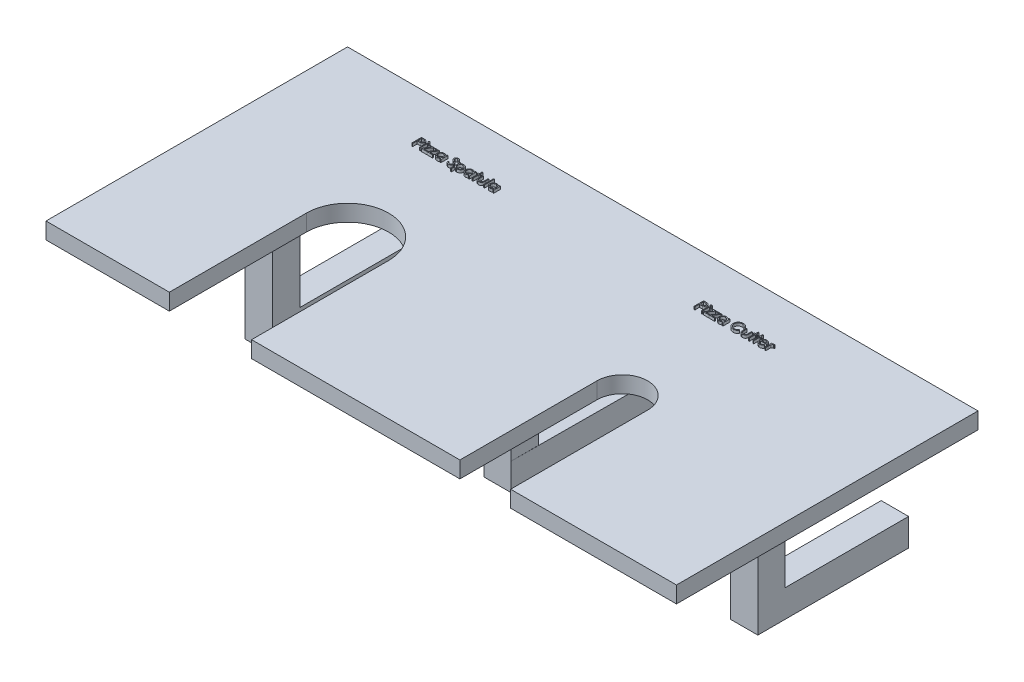
SolidWorks part; units mm, degrees
ref_plane "Front Plane" through (0, 0, 0) normal (0, 0, 1) x (1, 0, 0)
ref_plane "Top Plane" through (0, 0, 0) normal (0, 1, 0) x (1, 0, 0)
ref_plane "Right Plane" through (0, 0, 0) normal (1, 0, 0) x (0, 0, -1)
sketch "Sketch2" plane through (0, 0, 0) normal (0, 1, 0) x (1, 0, 0)
  line L0 (-88.9219, -70.4554) -> (-43.9219, -70.4554)
  line L1 (-88.9219, 39.5446) -> (141.0781, 39.5446)
  line L2 (-88.9219, 39.5446) -> (-88.9219, -70.4554)
  line L4 (141.0781, 39.5446) -> (141.0781, -70.4554)
  line L5 (-13.9219, -70.4554) -> (62.0781, -70.4554)
  line L6 (80.5781, -70.4554) -> (141.0781, -70.4554)
  line L8 (-43.9219, -70.4554) -> (-43.9219, -20.4554)
  line L9 (62.0781, -70.4554) -> (62.0781, -20.4554)
  line L12 (-13.9219, -20.4554) -> (-13.9219, -70.4554)
  line L13 (80.5781, -20.4554) -> (80.5781, -70.4554)
  arc A0 (-43.9219, -20.4554) -> (-13.9219, -20.4554) centre (-28.9219, -20.4554) cw
  arc A1 (62.0781, -20.4554) -> (80.5781, -20.4554) centre (71.3281, -20.4554) cw
  dimension "D1" = 230
  dimension "D2" = 110
extrude "Boss-Extrude2" add sketch "Sketch2" along normal blind 6
sketch3d "3DSketch1" plane through (0, 0, 0) normal (0, 0, 1) x (1, 0, 0)
sketch "Sketch6" plane through (0, 0, 15.4554) normal (0, 0, 1) x (1, 0, 0)
  line L5 (-71.2766, 0) -> (-61.2766, 0)
  line L6 (15.7975, 0) -> (25.7975, 0)
  line L7 (-88.9219, 0) -> (-43.9219, 0) construction
  line L8 (-71.2766, 0) -> (-71.2766, -40)
  line L9 (-71.2766, -40) -> (-61.2766, -40)
  line L10 (-61.2766, -40) -> (-61.2766, 0)
  line L12 (105.7606, 0) -> (115.7606, 0)
  line L14 (-13.9219, 0) -> (62.0781, 0) construction
  line L15 (15.7975, 0) -> (15.7975, -40)
  line L16 (15.7975, -40) -> (25.7975, -40)
  line L17 (25.7975, -40) -> (25.7975, 0)
  line L20 (80.5781, 0) -> (141.0781, 0) construction
  line L21 (105.7606, 0) -> (105.7606, -40)
  line L22 (105.7606, -40) -> (115.7606, -40)
  line L23 (115.7606, -40) -> (115.7606, 0)
extrude "Boss-Extrude3" add sketch "Sketch6" against normal blind 10
sketch3d "3DSketch5" plane through (0, 0, 0) normal (0, 0, 1) x (1, 0, 0)
sketch "Sketch8" plane through (0, -40, 0) normal (0, 1, 0) x (1, 0, 0)
  line L0 (-71.2766, -15.4554) -> (-71.2766, 39.5446)
  line L1 (141.0781, 39.5446) -> (-88.9219, 39.5446) construction
  line L2 (-71.2766, 39.5446) -> (-61.2766, 39.5446)
  line L3 (-61.2766, 39.5446) -> (-61.2766, -15.4554)
  line L4 (-61.2766, -5.4554) -> (-61.2766, -15.4554) construction
  line L5 (-61.2766, -15.4554) -> (-71.2766, -15.4554)
  line L6 (15.7975, -15.4554) -> (15.7975, 39.5446)
  line L7 (15.7975, -5.4554) -> (15.7975, -15.4554) construction
  line L8 (15.7975, 39.5446) -> (26.0781, 39.5446)
  line L9 (26.0781, 39.5446) -> (25.7975, -15.4554)
  line L10 (25.7975, -15.4554) -> (15.7975, -15.4554)
  line L11 (105.7606, -15.4554) -> (105.7606, 39.5446)
  line L12 (105.7606, 39.5446) -> (115.7606, 39.5446)
  line L13 (115.7606, 39.5446) -> (115.7606, -15.4554)
  line L14 (115.7606, -15.4554) -> (105.7606, -15.4554)
extrude "Boss-Extrude4" add sketch "Sketch8" against normal blind 10
sketch "Sketch9" plane through (0, 6, 0) normal (0, 1, 0) x (1, 0, 0)
  text T0 "Pizza Cutter\r\n"
  text T1 "Pizza Spatula"
extrude "Boss-Extrude8" add sketch "Sketch9" along normal blind 1
